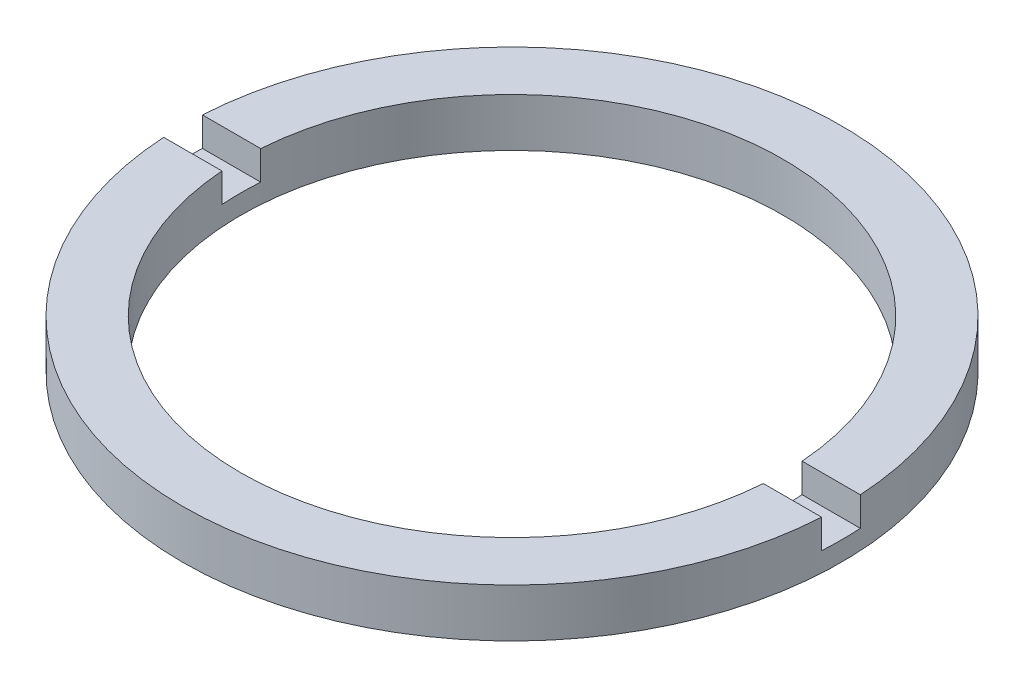
SolidWorks part; units mm, degrees
ref_plane "前视基准面" through (0, 0, 0) normal (0, 0, 1) x (1, 0, 0)
ref_plane "上视基准面" through (0, 0, 0) normal (0, 1, 0) x (1, 0, 0)
ref_plane "右视基准面" through (0, 0, 0) normal (1, 0, 0) x (0, 0, -1)
sketch "草图1" plane through (0, 0, 0) normal (0, 0, 1) x (1, 0, 0)
  line L0 (0, 56.2608) -> (0, -99.1922) construction
  line L1 (14, -1.9642) -> (17, -1.9642)
  line L4 (17, -1.9642) -> (17, -4.4642)
  line L5 (14, -4.4642) -> (14, -1.9642)
  line L7 (14, -4.4642) -> (17, -4.4642)
  dimension "D1" = 2.5
  dimension "D2" = 17
  dimension "D3" = 14
revolve "旋转1" add sketch "草图1" angle 360 about L0
cosmetic thread "装饰螺纹线1" parameters "D2"=33.999
sketch "草图2" plane through (0, -1.9642, 0) normal (0, 1, 0) x (1, 0, 0)
  line L0 (-28.67, 0) -> (29.9422, 0) construction
  line L2 (-26.8525, 1) -> (26.8525, 1)
  line L3 (-26.8525, 1) -> (-26.8525, -1)
  line L4 (-26.8525, -1) -> (26.8525, -1)
  line L5 (26.8525, 1) -> (26.8525, -1)
  line L6 (-26.8525, 1) -> (26.8525, -1) construction
  line L7 (-26.8525, -1) -> (26.8525, 1) construction
  point P3 (0, 0)
  dimension "D1" = 2
extrude "切除-拉伸1" cut sketch "草图2" against normal blind 1.5
